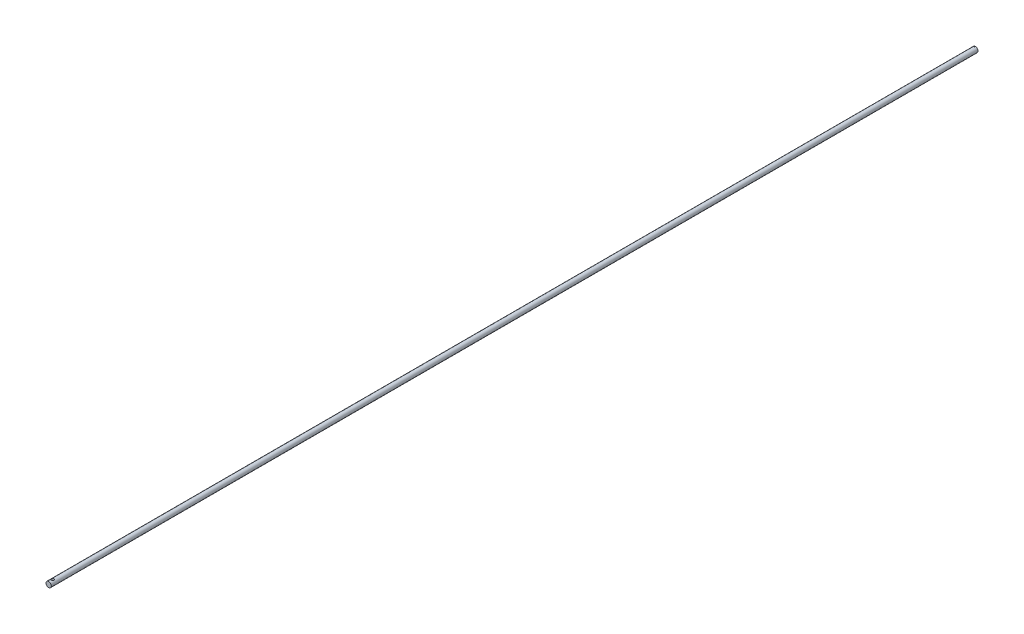
SolidWorks part; units mm, degrees
material "1060 Alloy"
ref_plane "Front Plane" through (0, 0, 0) normal (0, 0, 1) x (1, 0, 0)
ref_plane "Top Plane" through (0, 0, 0) normal (0, 1, 0) x (1, 0, 0)
ref_plane "Right Plane" through (0, 0, 0) normal (1, 0, 0) x (0, 0, -1)
sketch "Sketch1" plane through (0, 0, 0) normal (0, 0, 1) x (1, 0, 0)
  circle A0 centre (0, 0) radius 2.413
  dimension "D1" = 4.826
extrude "Boss-Extrude1" add sketch "Sketch1" along normal blind 847.09
sketch "Sketch2" plane through (0, 0, 0) normal (0, 1, 0) x (1, 0, 0)
  line L1 (-2.413, -847.09) -> (2.413, -847.09) construction
  circle A0 centre (0, -843.556) radius 1.27
  circle A1 centre (0, -0.7358) radius 0.2809
  dimension "D1" = 2.54
  dimension "D2" = 3.534
extrude "Cut-Extrude1" cut sketch "Sketch2" against normal through all both and the other way through all
